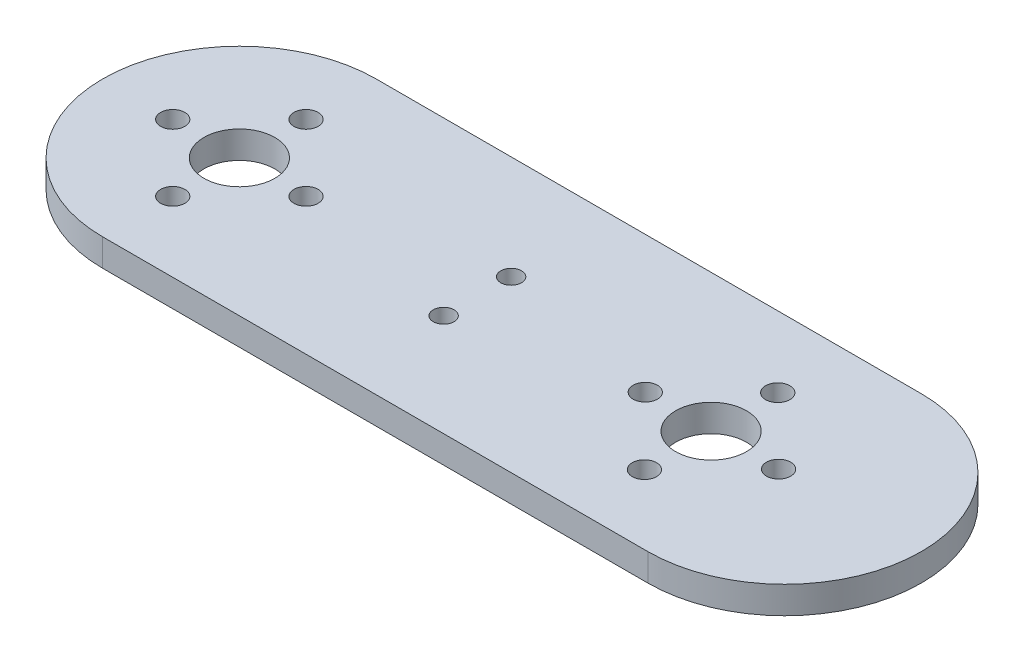
SolidWorks part; units mm, degrees
ref_plane "Front Plane" through (0, 0, 0) normal (0, 0, 1) x (1, 0, 0)
ref_plane "Top Plane" through (0, 0, 0) normal (0, 1, 0) x (1, 0, 0)
ref_plane "Right Plane" through (0, 0, 0) normal (1, 0, 0) x (0, 0, -1)
sketch "Sketch1" plane through (0, 0, 0) normal (0, 1, 0) x (1, 0, 0)
  line L0 (0, 15.5) -> (0, -15.5) construction
  line L1 (-15.5, 0) -> (15.5, 0) construction
  line L2 (-2.4674, 13.4022) -> (-4, 4) construction
  line L3 (4, -4) -> (-4, -4) construction
  line L4 (4, -4) -> (4, 4) construction
  line L5 (4, 4) -> (-4, 4) construction
  line L6 (-4, -4) -> (-4, 4) construction
  line L7 (4, -4) -> (-4, 4) construction
  line L8 (4, 4) -> (-4, -4) construction
  line L9 (-4, 4) -> (-2.4674, 13.4022)
  line L10 (4, 4) -> (2.4674, 13.4022)
  line L11 (4, -4) -> (2.4674, -13.4022)
  line L12 (-4, -4) -> (-2.4674, -13.4022)
  line L13 (-4, 4) -> (-12.5927, 2.4331) construction
  line L14 (-4, 4) -> (-12.4485, 2.4594)
  line L15 (-4, -4) -> (-12.4485, -2.4594)
  line L16 (4, -4) -> (12.4485, -2.4594)
  line L17 (4, 4) -> (12.4485, 2.4594)
  circle A0 centre (0, 0) radius 15.5 construction
  circle A1 centre (0, 0) radius 14.5 construction
  arc A2 (2.4674, 13.4022) -> (-2.4674, 13.4022) centre (0, 13) ccw
  arc A3 (2.4674, -13.4022) -> (-2.4674, -13.4022) centre (0, -13) cw
  arc A4 (-12.4485, 2.4594) -> (-12.4485, -2.4594) centre (-12, 0) ccw
  arc A5 (12.4485, 2.4594) -> (12.4485, -2.4594) centre (12, 0) cw
  circle A6 centre (0, 0) radius 12 construction
  circle A7 centre (0, 0) radius 9.5 construction
  circle A8 centre (0, 0) radius 7.5 construction
  circle A9 centre (0, 12) radius 0.5
  circle A10 centre (0, 9.5) radius 0.5
  circle A11 centre (0, 7.5) radius 0.5
  circle A12 centre (12, 0) radius 0.5
  circle A13 centre (9.5, 0) radius 0.5
  circle A14 centre (7.5, 0) radius 0.5
  circle A15 centre (0, -12) radius 0.5
  circle A16 centre (0, -9.5) radius 0.5
  circle A17 centre (0, -7.5) radius 0.5
  circle A18 centre (-12, 0) radius 0.5
  circle A19 centre (-9.5, 0) radius 0.5
  circle A20 centre (-7.5, 0) radius 0.5
  circle A21 centre (0, 0) radius 1.375
  point P59 (0, 0)
  dimension "D1" = 31
  dimension "D2" = 1
  dimension "D3" = 5
  dimension "D4" = 5
  dimension "D5" = 8
  dimension "D6" = 8
  dimension "D7" = 15
  dimension "D9" = 24
  dimension "D11" = 1
  dimension "D12" = 1
  dimension "D13" = 4
  dimension "D8" = 19
  dimension "D10" = 1
  dimension "D14" = 2.75
extrude "Boss-Extrude1" add sketch "Sketch1" along normal blind 2
sketch "Sketch4" plane through (0, 0, 0) normal (0, -1, 0) x (1, 0, 0)
  circle A0 centre (0, 0) radius 4.627
  circle A1 centre (0, 0) radius 2.627
  dimension "D1" = 9.254
  dimension "D2" = 2
extrude "Boss-Extrude3" add sketch "Sketch4" along normal blind 2.5
sketch "Sketch5" plane through (0, -2.5, 0) normal (0, -1, 0) x (1, 0, 0)
  line L0 (0, 0) -> (0, 0.6245) construction
  line L1 (0, 3.1016) -> (-0.2828, 2.6117)
  line L2 (0, 3.1016) -> (0.2828, 2.6117)
  line L3 (0.9584, 2.9498) -> (0.5381, 2.5713)
  line L4 (0.9584, 2.9498) -> (1.076, 2.3965)
  line L5 (1.8231, 2.5092) -> (1.3063, 2.2792)
  line L6 (1.8231, 2.5092) -> (1.7639, 1.9467)
  line L7 (2.5092, 1.8231) -> (1.9467, 1.7639)
  line L8 (2.5092, 1.8231) -> (2.2792, 1.3063)
  line L9 (2.9498, 0.9584) -> (2.3965, 1.076)
  line L10 (2.9498, 0.9584) -> (2.5713, 0.5381)
  line L11 (3.1016, 0) -> (2.6117, 0.2828)
  line L12 (3.1016, 0) -> (2.6117, -0.2828)
  line L13 (2.9498, -0.9584) -> (2.5713, -0.5381)
  line L14 (2.9498, -0.9584) -> (2.3965, -1.076)
  line L15 (2.5092, -1.8231) -> (2.2792, -1.3063)
  line L16 (2.5092, -1.8231) -> (1.9467, -1.7639)
  line L17 (1.8231, -2.5092) -> (1.7639, -1.9467)
  line L18 (1.8231, -2.5092) -> (1.3063, -2.2792)
  line L19 (0.9584, -2.9498) -> (1.076, -2.3965)
  line L20 (0.9584, -2.9498) -> (0.5381, -2.5713)
  line L21 (0, -3.1016) -> (0.2828, -2.6117)
  line L22 (0, -3.1016) -> (-0.2828, -2.6117)
  line L23 (-0.9584, -2.9498) -> (-0.5381, -2.5713)
  line L24 (-0.9584, -2.9498) -> (-1.076, -2.3965)
  line L25 (-1.8231, -2.5092) -> (-1.3063, -2.2792)
  line L26 (-1.8231, -2.5092) -> (-1.7639, -1.9467)
  line L27 (-2.5092, -1.8231) -> (-1.9467, -1.7639)
  line L28 (-2.5092, -1.8231) -> (-2.2792, -1.3063)
  line L29 (-2.9498, -0.9584) -> (-2.3965, -1.076)
  line L30 (-2.9498, -0.9584) -> (-2.5713, -0.5381)
  line L31 (-3.1016, 0) -> (-2.6117, -0.2828)
  line L32 (-3.1016, 0) -> (-2.6117, 0.2828)
  line L33 (-2.9498, 0.9584) -> (-2.5713, 0.5381)
  line L34 (-2.9498, 0.9584) -> (-2.3965, 1.076)
  line L35 (-2.5092, 1.8231) -> (-2.2792, 1.3063)
  line L36 (-2.5092, 1.8231) -> (-1.9467, 1.7639)
  line L37 (-1.8231, 2.5092) -> (-1.7639, 1.9467)
  line L38 (-1.8231, 2.5092) -> (-1.3063, 2.2792)
  line L39 (-0.9584, 2.9498) -> (-1.076, 2.3965)
  line L40 (-0.9584, 2.9498) -> (-0.5381, 2.5713)
  circle A0 centre (0, 0) radius 2.627 construction
  arc A1 (-2.2792, 1.3063) -> (-2.3965, 1.076) centre (0, 0) ccw
  arc A2 (-1.7639, 1.9467) -> (-1.9467, 1.7639) centre (0, 0) ccw
  arc A3 (-1.076, 2.3965) -> (-1.3063, 2.2792) centre (0, 0) ccw
  arc A4 (-0.2828, 2.6117) -> (-0.5381, 2.5713) centre (0, 0) ccw
  arc A5 (0.5381, 2.5713) -> (0.2828, 2.6117) centre (0, 0) ccw
  arc A6 (1.3063, 2.2792) -> (1.076, 2.3965) centre (0, 0) ccw
  arc A7 (1.9467, 1.7639) -> (1.7639, 1.9467) centre (0, 0) ccw
  arc A8 (2.3965, 1.076) -> (2.2792, 1.3063) centre (0, 0) ccw
  arc A9 (2.6117, 0.2828) -> (2.5713, 0.5381) centre (0, 0) ccw
  arc A10 (2.5713, -0.5381) -> (2.6117, -0.2828) centre (0, 0) ccw
  arc A11 (2.2792, -1.3063) -> (2.3965, -1.076) centre (0, 0) ccw
  arc A12 (1.7639, -1.9467) -> (1.9467, -1.7639) centre (0, 0) ccw
  arc A13 (1.076, -2.3965) -> (1.3063, -2.2792) centre (0, 0) ccw
  arc A14 (0.2828, -2.6117) -> (0.5381, -2.5713) centre (0, 0) ccw
  arc A15 (-0.5381, -2.5713) -> (0, -2.627) centre (0, 0) ccw
  arc A16 (-1.3063, -2.2792) -> (-1.076, -2.3965) centre (0, 0) ccw
  arc A17 (-1.9467, -1.7639) -> (-1.7639, -1.9467) centre (0, 0) ccw
  arc A18 (-2.3965, -1.076) -> (-2.2792, -1.3063) centre (0, 0) ccw
  arc A19 (-2.6117, -0.2828) -> (-2.5713, -0.5381) centre (0, 0) ccw
  arc A20 (-2.5713, 0.5381) -> (-2.6117, 0.2828) centre (0, 0) ccw
  point P68 (0, 0)
  circle M5 centre (0, 0) radius 2.627
  dimension "D1" = 30
  dimension "D2" = 3.1016
  dimension "D3" = 20
extrude "Cut-Extrude3" cut sketch "Sketch5" against normal up to surface (2.5 mm away) contours L36 L35 M5 | L34 L33 M5 | L32 L31 M5 | L30 L29 M5 | L28 L27 M5 | L26 L25 M5 | L24 L23 M5 | L0 L21 M5 | L22 L0 M5 | L20 L19 M5 | L18 L17 M5 | L16 L15 M5 | L14 L13 M5 | L12 L11 M5 | L10 L9 M5 | L8 L7 M5 | L6 L5 M5 | L4 L3 M5 | L0 L2 M5 | L0 L1 M5 | L40 L39 M5 | L38 L37 M5
sketch "Sketch6" plane through (0, 2, 0) normal (0, 1, 0) x (1, 0, 0)
  circle A0 centre (0, 0) radius 20.066
  circle A2 centre (0, 0) radius 3.75
  dimension "D1" = 40.132
extrude "Boss-Extrude6" add sketch "Sketch6" against normal blind 2.54
sketch "Sketch7" plane through (0, 2, 0) normal (0, 1, 0) x (1, 0, 0)
  circle A0 centre (0, 9.779) radius 1.778
extrude "Cut-Extrude4" cut sketch "Sketch7" against normal blind 2.54
pattern_circular "CirPattern1" count 4 over 360 about axis through (0, 0, 0) along (0, 1, 0) of "Cut-Extrude4"
sketch "Esquisse1" plane through (0, 2, 0) normal (0, 1, 0) x (1, 0, 0)
  line L0 (0, 20.066) -> (80.01, 20.066)
  line L1 (0, -20.066) -> (80.01, -20.066)
  circle A0 centre (0, 0) radius 20.066 construction
  arc A1 (80.01, 20.066) -> (80.01, -20.066) centre (80.01, 0) cw
  arc A2 (0, -20.066) -> (0, 20.066) centre (0, 0) ccw
  dimension "D1" = 80.01
  dimension "D2" = 80.01
extrude "Boss.-Extru.1" add sketch "Esquisse1" along normal blind 2.2225 and the other way blind 2.54 contours L1 A1 L0 A2
sketch "Esquisse3" plane through (0, 2, 0) normal (0, 1, 0) x (1, 0, 0)
  circle A0 centre (0, 0) radius 20.066
  circle A1 centre (9.779, 0) radius 1.778
  circle A2 centre (0, 9.779) radius 1.778
  circle A3 centre (-9.779, 0) radius 1.778
  circle A4 centre (0, -9.779) radius 1.778
  circle A5 centre (0, 0) radius 1.375
extrude "Boss.-Extru.2" add sketch "Esquisse3" along normal blind 2.2225
sketch "Esquisse4" plane through (0, -0.54, 0) normal (0, -1, 0) x (1, 0, 0)
  line L0 (0, 20.066) -> (80.01, 20.066) construction
  line L1 (80.01, 10.16) -> (39.116, 10.16)
  line L2 (39.116, 10.16) -> (39.116, -9.906)
  line L3 (39.116, -9.906) -> (80.01, -9.906)
  line L4 (80.01, -9.906) -> (80.01, 10.16)
  dimension "D1" = 9.906
  dimension "D2" = 20.066
  dimension "D3" = 40.894
extrude "Enlèv. mat.-Extru.1" cut sketch "Esquisse4" against normal up to next
sketch "Esquisse5" plane through (0, -0.54, 0) normal (0, -1, 0) x (-1, 0, 0)
  line L0 (-39.116, -10.16) -> (-39.116, 9.906) construction
  line L1 (-39.116, 9.906) -> (-80.01, 9.906) construction
  line L2 (-80.01, -10.16) -> (-39.116, -10.16) construction
  line L3 (-80.01, 9.906) -> (-80.01, -10.16) construction
  circle A0 centre (-35.052, -5.08) radius 1.524
  circle A1 centre (-35.052, 4.826) radius 1.524
  circle A2 centre (-84.074, -5.08) radius 1.524
  circle A3 centre (-84.074, 4.826) radius 1.524
  dimension "D2" = 4.064
  dimension "D3" = 5.08
  dimension "D4" = 5.08
  dimension "D5" = 5.08
  dimension "D6" = 5.08
  dimension "D7" = 4.064
  dimension "D8" = 4.064
  dimension "D9" = 3.048
  dimension "D10" = 3.048
  dimension "D11" = 3.048
  dimension "D12" = 3.048
  dimension "D1" = 4.064
extrude "Enlèv. mat.-Extru.2" cut sketch "Esquisse5" against normal through all
sketch "Esquisse6" plane through (0, 4.2225, 0) normal (0, 1, 0) x (1, 0, 0)
  line L1 (-24.0414, -40.1247) -> (105.7665, -40.1247)
  line L2 (-24.0414, -40.1247) -> (-24.0414, 44.3818)
  line L3 (-24.0414, 44.3818) -> (105.7665, 44.3818)
  line L4 (105.7665, -40.1247) -> (105.7665, 44.3818)
extrude "Enlèv. mat.-Extru.3" cut sketch "Esquisse6" against normal blind 0.76
sketch "Esquisse7" plane through (0, -2.5, 0) normal (0, -1, 0) x (-1, 0, 0)
  circle A0 centre (0, 0) radius 5.2
  dimension "D1" = 10.4
extrude "Enlèv. mat.-Extru.4" cut sketch "Esquisse7" against normal through all
sketch "Esquisse8" plane through (0, -0.54, 0) normal (0, -1, 0) x (-1, 0, 0)
  line L1 (-39.116, 9.906) -> (-80.01, 9.906)
  line L2 (-39.116, 9.906) -> (-39.116, -10.16)
  line L3 (-39.116, -10.16) -> (-80.01, -10.16)
  line L4 (-80.01, 9.906) -> (-80.01, -10.16)
extrude "Boss.-Extru.3" add sketch "Esquisse8" against normal through all
sketch "Esquisse9" plane through (0, -0.54, 0) normal (0, -1, 0) x (-1, 0, 0)
  circle A0 centre (-69.344, -0.125) radius 5.2
  circle A1 centre (-84.074, -5.08) radius 1.524 construction
  dimension "D1" = 14.73
  dimension "D2" = 10.4
  dimension "D3" = 4.955
extrude "Enlèv. mat.-Extru.5" cut sketch "Esquisse9" against normal blind 10 contours A0
sketch "Esquisse11" plane through (0, 3.4625, 0) normal (0, 1, 0) x (1, 0, 0)
  circle A0 centre (69.344, 9.655) radius 1.78
  circle A2 centre (69.344, -9.905) radius 1.78
  circle A3 centre (59.564, 0) radius 1.78
  circle A5 centre (79.124, 0) radius 1.78
  circle A6 centre (69.344, -0.125) radius 5.2 construction
  dimension "D1" = 9.78
  dimension "D2" = 9.78
  dimension "D3" = 9.78
  dimension "D4" = 9.78
  dimension "D7" = 3.56
  dimension "D8" = 3.56
  dimension "D9" = 3.56
  dimension "D10" = 3.56
  dimension "D5" = 0
  dimension "D6" = 0
extrude "Enlèv. mat.-Extru.6" cut sketch "Esquisse11" against normal blind 10
sketch "Esquisse10" plane through (0, 3.4625, 0) normal (0, 1, 0) x (1, 0, 0)
  circle A4 centre (84.074, 4.826) radius 1.524
  circle A5 centre (84.074, -5.08) radius 1.524
extrude "Boss.-Extru.4" add sketch "Esquisse10" against normal through all
